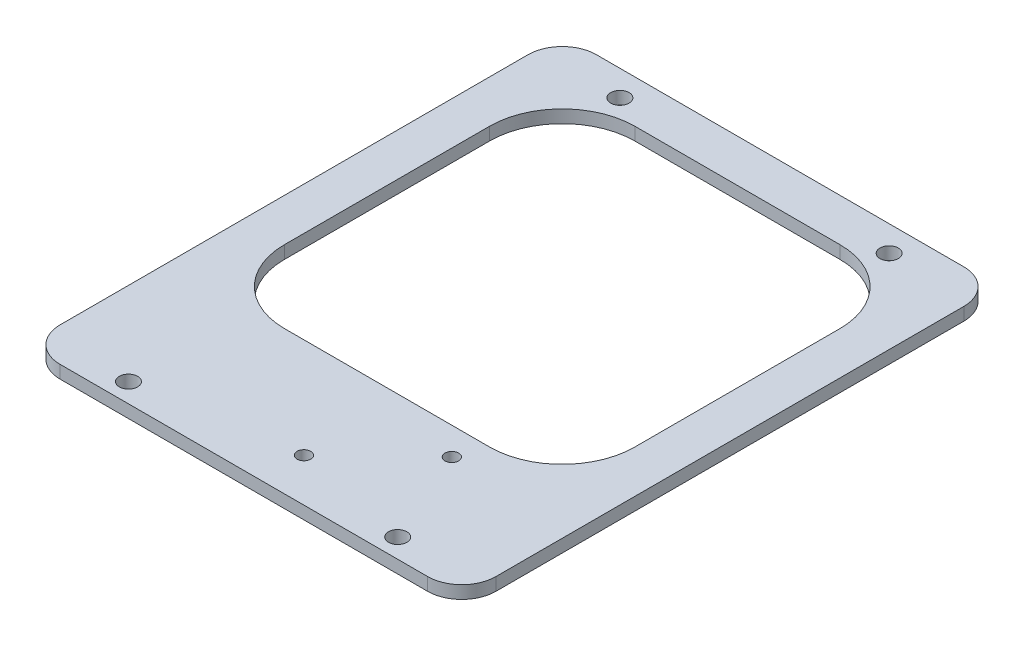
SolidWorks part; units mm, degrees
ref_plane "Front Plane" through (0, 0, 0) normal (0, 0, 1) x (1, 0, 0)
ref_plane "Top Plane" through (0, 0, 0) normal (0, 1, 0) x (1, 0, 0)
ref_plane "Right Plane" through (0, 0, 0) normal (1, 0, 0) x (0, 0, -1)
sketch "Sketch1" plane through (0, 0, 0) normal (0, 1, 0) x (1, 0, 0)
  line L0 (-43, 51) -> (43, 51)
  line L5 (51, 43) -> (51, -66.5)
  line L6 (43, -74.5) -> (-43, -74.5)
  line L11 (-51, -66.5) -> (-51, 43)
  line L12 (0, 0) -> (51, 0) construction
  line L13 (0, 0) -> (0, -16.8172) construction
  arc A8 (-43, -74.5) -> (-51, -66.5) centre (-43, -66.5) cw
  arc A9 (51, -66.5) -> (43, -74.5) centre (43, -66.5) cw
  arc A10 (43, 51) -> (51, 43) centre (43, 43) cw
  arc A11 (-43, 51) -> (-51, 43) centre (-43, 43) ccw
  circle A12 centre (-31.5, 45) radius 2.15
  circle A13 centre (31.5, 45) radius 2.15
  circle A14 centre (-31.5, -70) radius 2.15
  circle A15 centre (31.5, -70) radius 2.15
  point P3 (0, 51)
  point P12 (51, -74.5)
  point P15 (51, 51)
  point P18 (-51, 51)
  dimension "D3" = 102
  dimension "D5" = 4.3
  dimension "D4" = 8
  dimension "D6" = 45
  dimension "D7" = 31.5
  dimension "D8" = 31.5
  dimension "D9" = 70
  dimension "D1" = 51
  dimension "D2" = 125.5
extrude "Boss-Extrude1" add sketch "Sketch1" along normal blind 3
sketch "Sketch3" plane through (0, 3, 0) normal (0, 1, 0) x (1, 0, 0)
  line L1 (-24, -41) -> (24, -41)
  line L2 (-41, -24) -> (-41, 24)
  line L3 (-24, 41) -> (24, 41)
  line L4 (41, -24) -> (41, 24)
  line L5 (-41, -41) -> (41, 41) construction
  line L6 (-41, 41) -> (41, -41) construction
  arc A0 (24, -41) -> (41, -24) centre (24, -24) ccw
  arc A1 (-24, -41) -> (-41, -24) centre (-24, -24) cw
  arc A2 (24, 41) -> (41, 24) centre (24, 24) cw
  arc A3 (-41, 24) -> (-24, 41) centre (-24, 24) cw
  point P0 (0, 0)
  dimension "D2" = 17
  dimension "D1" = 82
extrude "Cut-Extrude1" cut sketch "Sketch3" against normal up to next
sketch "Sketch5" plane through (0, 3, 0) normal (0, 1, 0) x (1, 0, 0)
  line L0 (0, 0) -> (0, -54.86) construction
  line L1 (0, -54.86) -> (47.7096, -38.4881) construction
  line L2 (0.6148, -54.649) -> (3.958, -64.3914) construction
  circle A0 centre (21.6129, -47.4434) radius 1.6
  circle A1 centre (3.958, -64.3914) radius 1.6
  dimension "D3" = 3.2
  dimension "D4" = 22.85
  dimension "D1" = 54.86
  dimension "D2" = 71.06
  dimension "D5" = 10.3
  dimension "D6" = 22.2
  dimension "D7" = 0.65
extrude "Cut-Extrude2" cut sketch "Sketch5" against normal up to next
